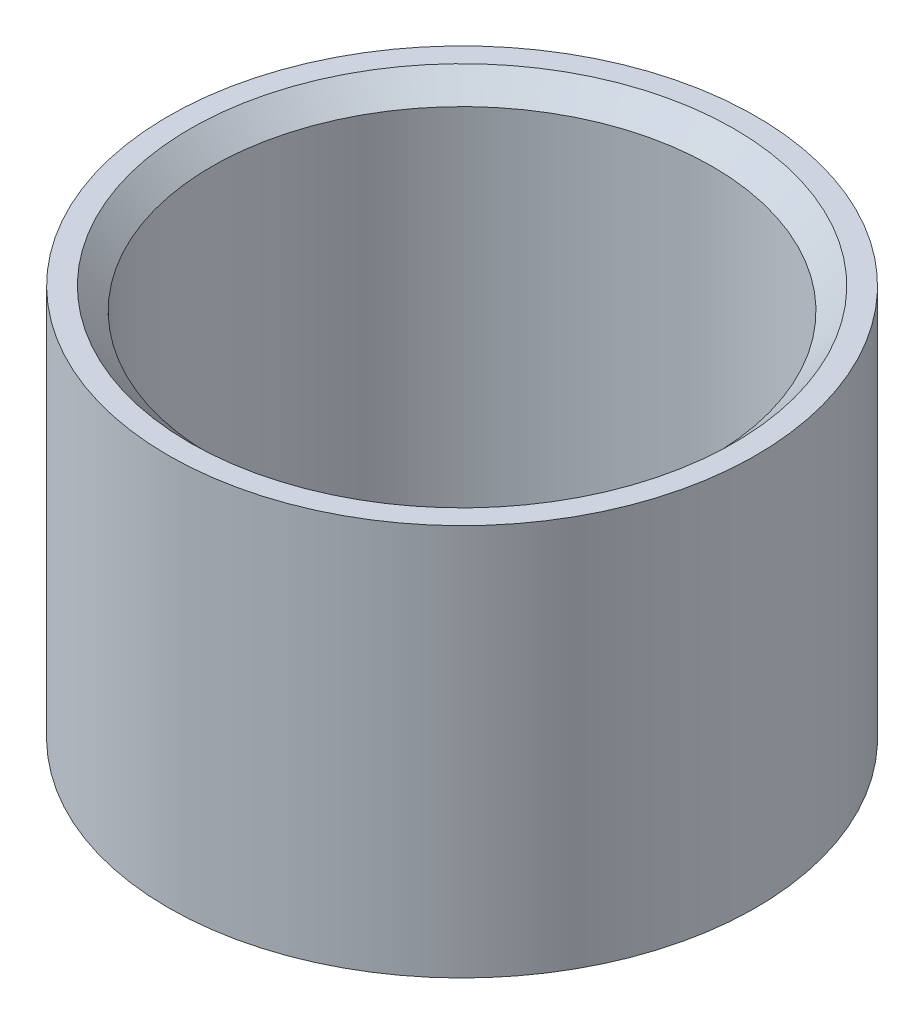
SolidWorks part; units mm, degrees
ref_plane "Front Plane" through (0, 0, 0) normal (0, 0, 1) x (1, 0, 0)
ref_plane "Top Plane" through (0, 0, 0) normal (0, 1, 0) x (1, 0, 0)
ref_plane "Right Plane" through (0, 0, 0) normal (1, 0, 0) x (0, 0, -1)
sketch "Sketch1" plane through (0, 0, 0) normal (0, 1, 0) x (1, 0, 0)
  circle A0 centre (0, 0) radius 1.35
  dimension "D1" = 2.7
extrude "Boss-Extrude1" add sketch "Sketch1" along normal blind 1.8
sketch "Sketch2" plane through (0, 1.8, 0) normal (0, 1, 0) x (1, 0, 0)
  circle A0 centre (0, 0) radius 1.15
  dimension "D1" = 2.3
extrude "Cut-Extrude1" cut sketch "Sketch2" against normal up to next
chamfer "Chamfer1" distance 0.1 angle 45 1 edges at (0, 1.8, 1.15)
